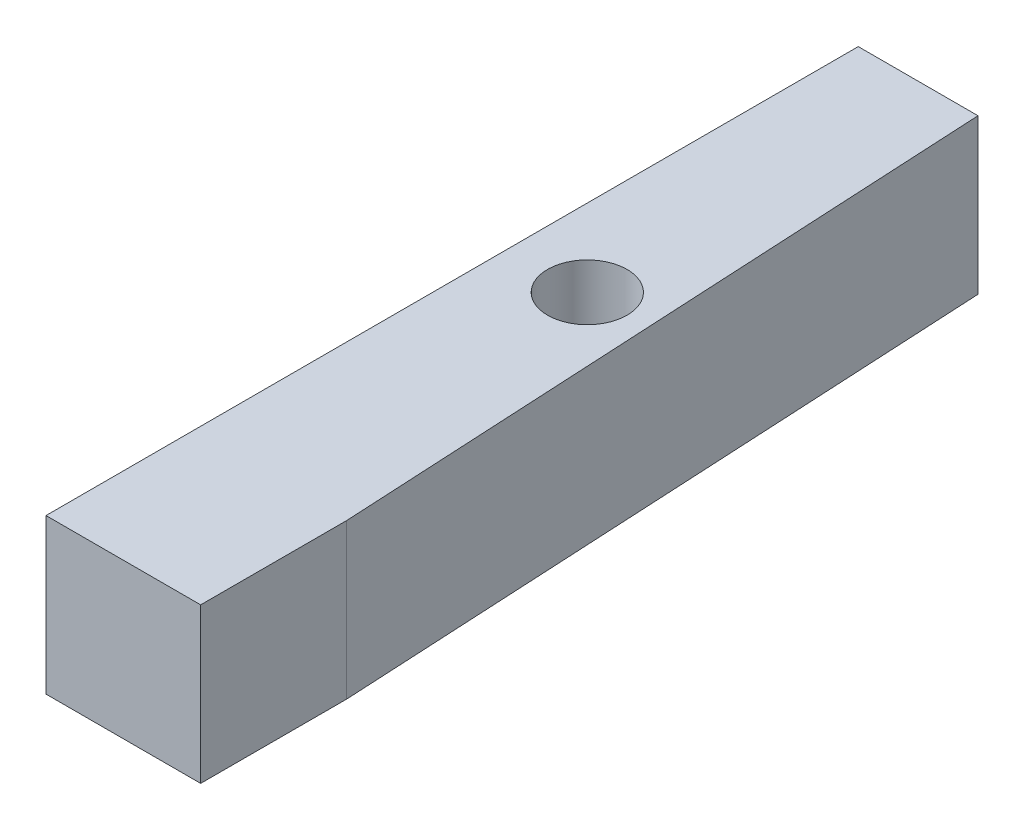
SolidWorks part; units mm, degrees
ref_plane "Front Plane" through (0, 0, 0) normal (0, 0, 1) x (1, 0, 0)
ref_plane "Top Plane" through (0, 0, 0) normal (0, 1, 0) x (1, 0, 0)
ref_plane "Right Plane" through (0, 0, 0) normal (1, 0, 0) x (0, 0, -1)
sketch "Sketch1" plane through (0, 0, 0) normal (0, 0, 1) x (1, 0, 0)
  line L1 (-12.7, -12.7) -> (12.7, -12.7)
  line L2 (-12.7, -12.7) -> (-12.7, 12.7)
  line L3 (-12.7, 12.7) -> (12.7, 12.7)
  line L4 (12.7, -12.7) -> (12.7, 12.7)
  line L5 (-12.7, -12.7) -> (12.7, 12.7) construction
  line L6 (-12.7, 12.7) -> (12.7, -12.7) construction
  point P0 (0, 0)
  dimension "D1" = 25.4
  dimension "D2" = 25.4
extrude "Boss-Extrude1" add sketch "Sketch1" against normal blind 133.4008
sketch "Sketch2" plane through (0, 12.7, 0) normal (0, 1, 0) x (1, 0, 0)
  line L0 (12.7, 0) -> (-12.7, 0) construction
  circle A0 centre (0, 76.2) radius 6.5243
  dimension "D1" = 76.2
extrude "Cut-Extrude2" cut sketch "Sketch2" against normal through all contours A0
sketch "Sketch3" plane through (0, 12.7, 0) normal (0, 1, 0) x (1, 0, 0)
  line L4 (6.9654, 133.4008) -> (15.24, -24.4877)
  line L15 (12.7, 133.4008) -> (6.9654, 133.4008)
  line L16 (12.7, 133.4008) -> (-12.7, 133.4008) construction
  line L17 (12.7, 133.4008) -> (12.7, 23.9784)
  line L18 (12.7, 133.4008) -> (12.7, 0) construction
extrude "Cut-Extrude3" cut sketch "Sketch3" against normal through all
equation "\"D2@Sketch1\"=\"D1@Sketch1\""
